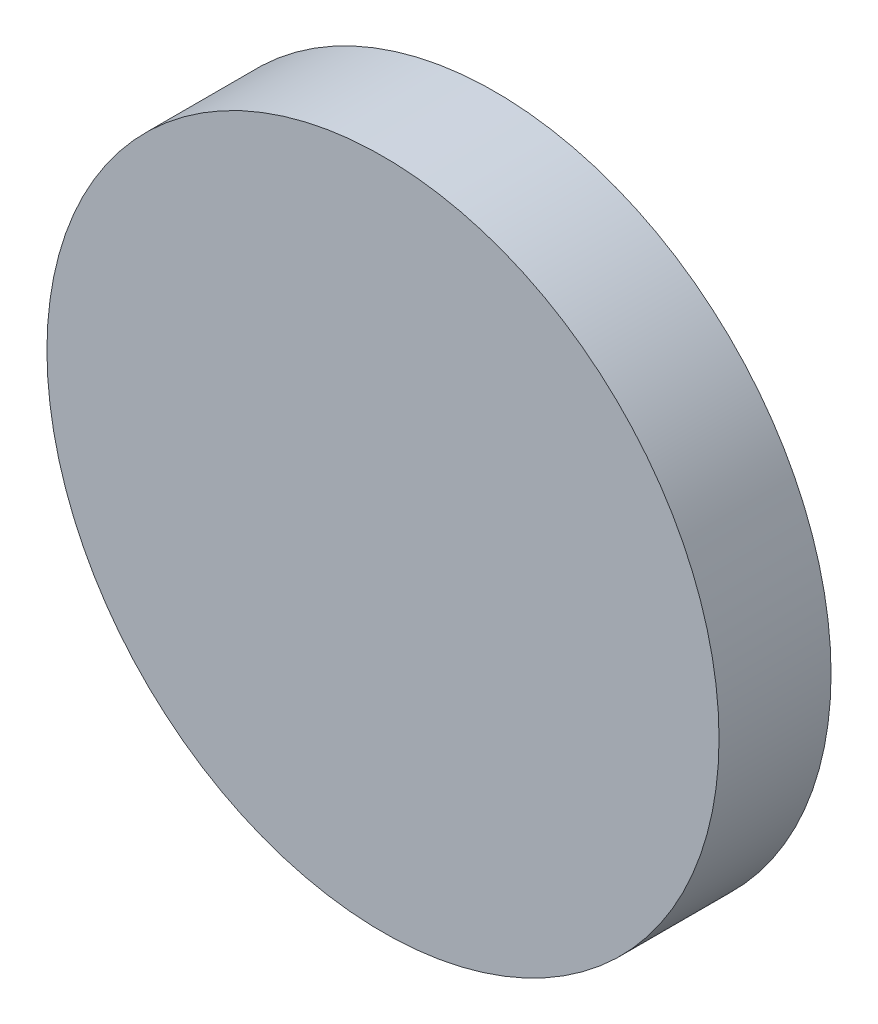
SolidWorks part; units mm, degrees
material "EPDM 60 硬度计"
ref_plane "前视基准面" through (0, 0, 0) normal (0, 0, 1) x (1, 0, 0)
ref_plane "上视基准面" through (0, 0, 0) normal (0, 1, 0) x (1, 0, 0)
ref_plane "右视基准面" through (0, 0, 0) normal (1, 0, 0) x (0, 0, -1)
sketch "草图1" plane through (0, 0, 0) normal (0, 0, 1) x (1, 0, 0)
  circle A0 centre (0, 0) radius 15
  dimension "D1" = 30
extrude "凸台-拉伸1" add sketch "草图1" along normal blind 5
